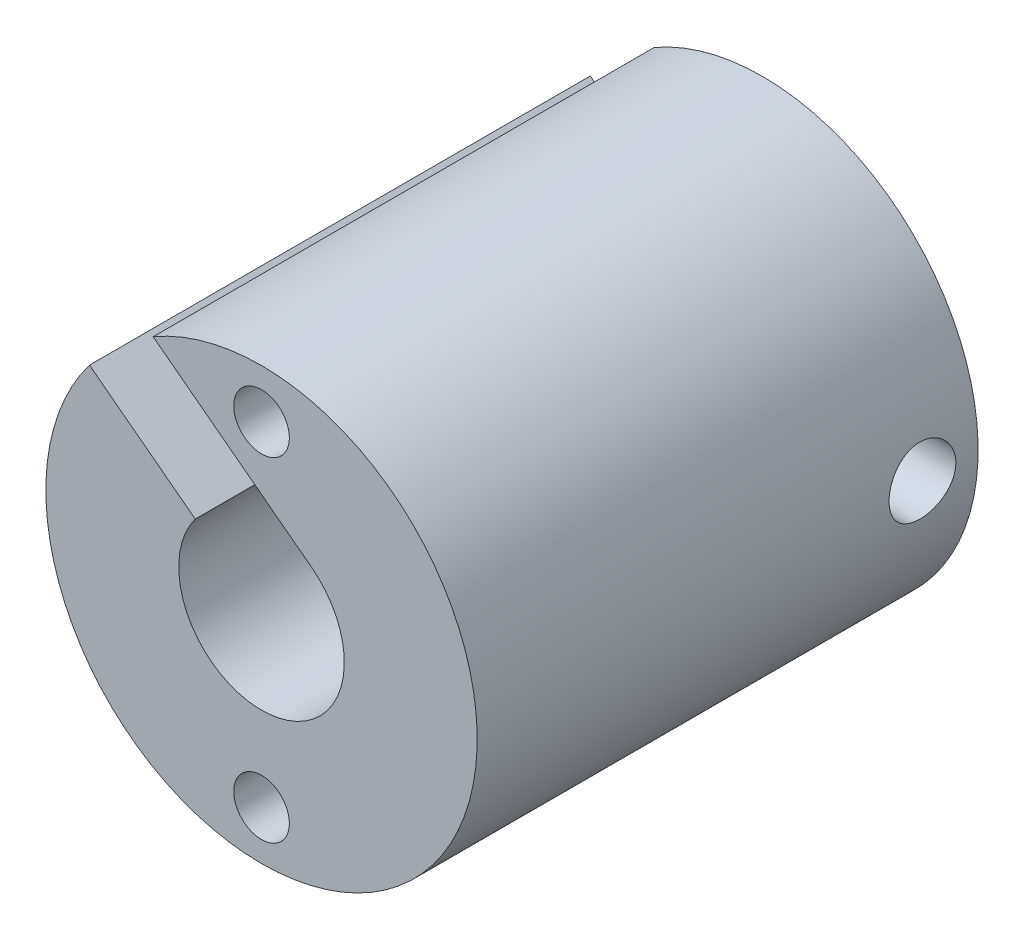
SolidWorks part; units mm, degrees
other "细节项目1"
material "6061-T6 (SS)"
ref_plane "前视基准面" through (0, 0, 0) normal (0, 0, 1) x (1, 0, 0)
ref_plane "上视基准面" through (0, 0, 0) normal (0, 1, 0) x (1, 0, 0)
ref_plane "右视基准面" through (0, 0, 0) normal (1, 0, 0) x (0, 0, -1)
sketch "草图1" plane through (0, 0, 0) normal (0, 0, 1) x (1, 0, 0)
  circle A0 centre (0, 0) radius 2.975
  circle A1 centre (0, 0) radius 7.75
  circle A2 centre (0, 0) radius 6 construction
  circle A3 centre (0, 6) radius 1
  circle A4 centre (0, -6) radius 1
  point P11 (0, 0)
  dimension "D1" = 5.95
  dimension "D2" = 15.5
  dimension "D3" = 12
  dimension "D4" = 2
  dimension "D5" = 2
extrude "凸台-拉伸1" add sketch "草图1" along normal blind 18
cosmetic thread "装饰螺纹线1" parameters "D1"=5, "D2"=2.5
cosmetic thread "装饰螺纹线2" parameters "D1"=5, "D2"=2.5
sketch "草图2" plane through (0, 0, 0) normal (1, 0, 0) x (0, 0, -1)
  line L0 (0, 0) -> (-2, 0) construction
  circle A0 centre (-2, 0) radius 1.2
  dimension "D2" = 2.4
  dimension "D1" = 2
extrude "切除-拉伸1" cut sketch "草图2" against normal through all both and the other way through all
cosmetic thread "装饰螺纹线3" parameters "D2"=3
cosmetic thread "装饰螺纹线4" parameters "D2"=3
sketch "草图3" plane through (0, 0, 0) normal (0, 0, -1) x (-1, 0, 0)
  line L4 (-1.8014, 2.3676) -> (3.8938, 6.7008)
  line L5 (3.8938, 6.7008) -> (6.1828, 6.7008)
  line L6 (6.1828, 6.7008) -> (6.1828, 4.6728)
  line L7 (6.1828, 4.6728) -> (2.3827, 1.7814)
  line L8 (2.3827, 1.7814) -> (-1.8014, 2.3676)
  circle A2 centre (0, 0) radius 2.975 construction
  circle A3 centre (0, 0) radius 7.75 construction
  circle A4 centre (0, 6) radius 1 construction
  dimension "D1" = 1.8
  dimension "D3" = 3
extrude "切除-拉伸2" cut sketch "草图3" against normal through all
